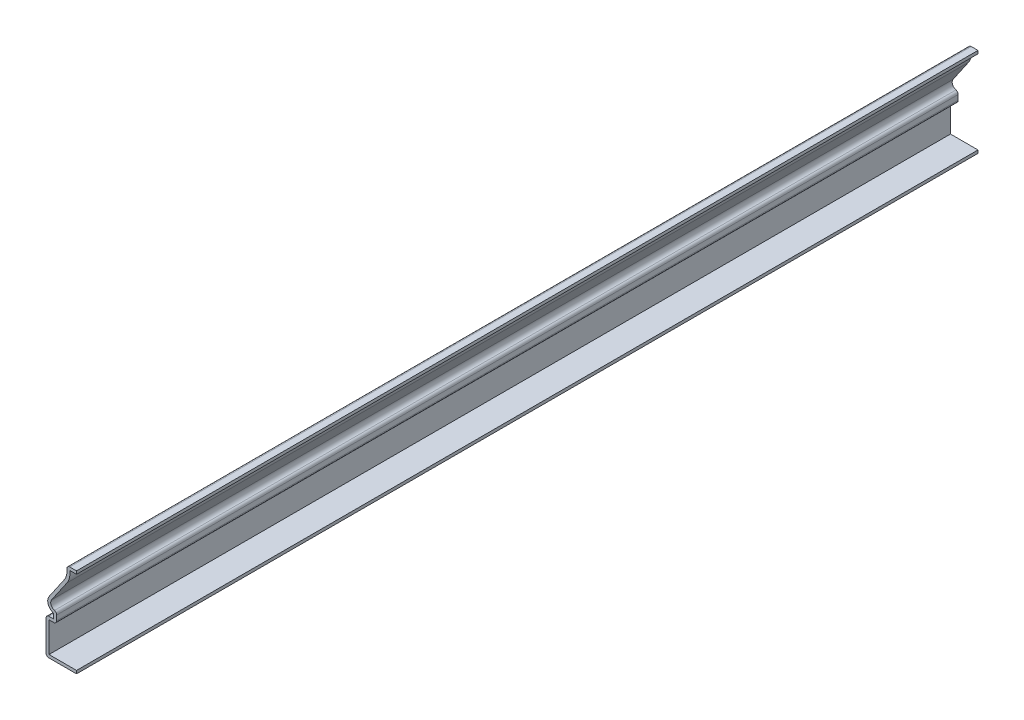
SolidWorks part; units mm, degrees
ref_plane "Front Plane" through (0, 0, 0) normal (0, 0, 1) x (1, 0, 0)
ref_plane "Top Plane" through (0, 0, 0) normal (0, 1, 0) x (1, 0, 0)
ref_plane "Right Plane" through (0, 0, 0) normal (1, 0, 0) x (0, 0, -1)
sketch "Sketch1" plane through (0, 0, 0) normal (0, 0, 1) x (1, 0, 0)
  line L0 (0, 0) -> (0, 30.1625) construction
  line L1 (0, 0) -> (-10.3187, 0)
  line L2 (-10.3187, 0) -> (-10.3187, 12.1995)
  line L3 (-10.3187, 12.1995) -> (-7.726, 12.1995)
  line L4 (-7.726, 12.1995) -> (-7.726, 13.8788)
  line L5 (-9.2609, 18.0517) -> (-4.0888, 25.5809)
  line L6 (0, 30.1625) -> (-3.5719, 30.1625)
  line L7 (0, 15.0812) -> (-14.3081, 15.0812) construction
  line L8 (-10.493, 1.3268) -> (-0.1742, 1.3268) construction
  arc A1 (-3.5719, 30.1625) -> (-4.0888, 25.5809) centre (-8.1296, 28.3568) cw
  arc A2 (-9.2609, 18.0517) -> (-7.726, 13.8788) centre (-7.0151, 16.509) ccw
  point P3 (-6.0179, 16.5577)
  point P10 (0, 0)
  point P15 (-7.0151, 16.509)
  point P16 (0, 0)
  point P17 (0, 0)
  point P20 (-4.6801, 24.5113)
  point P21 (-3.5719, 30.1625)
  point P22 (-8.1296, 28.3568)
  dimension "D1" = 30.1625
  dimension "D2" = 10.3187
  dimension "D3" = 3.5719
  dimension "D6" = 10.3187
extrude "Extrude-Thin1" add sketch "Sketch1" against normal blind 304.8 thin
fillet "Fillet1" radius 1.016 5 edges at (-10.3187, 0, -152.4) (-10.3187, 12.1995, -152.4) (-6.71, 11.1835, -152.4) (-6.71, 14.8279, -152.4) (-3.5719, 30.1625, -152.4)
